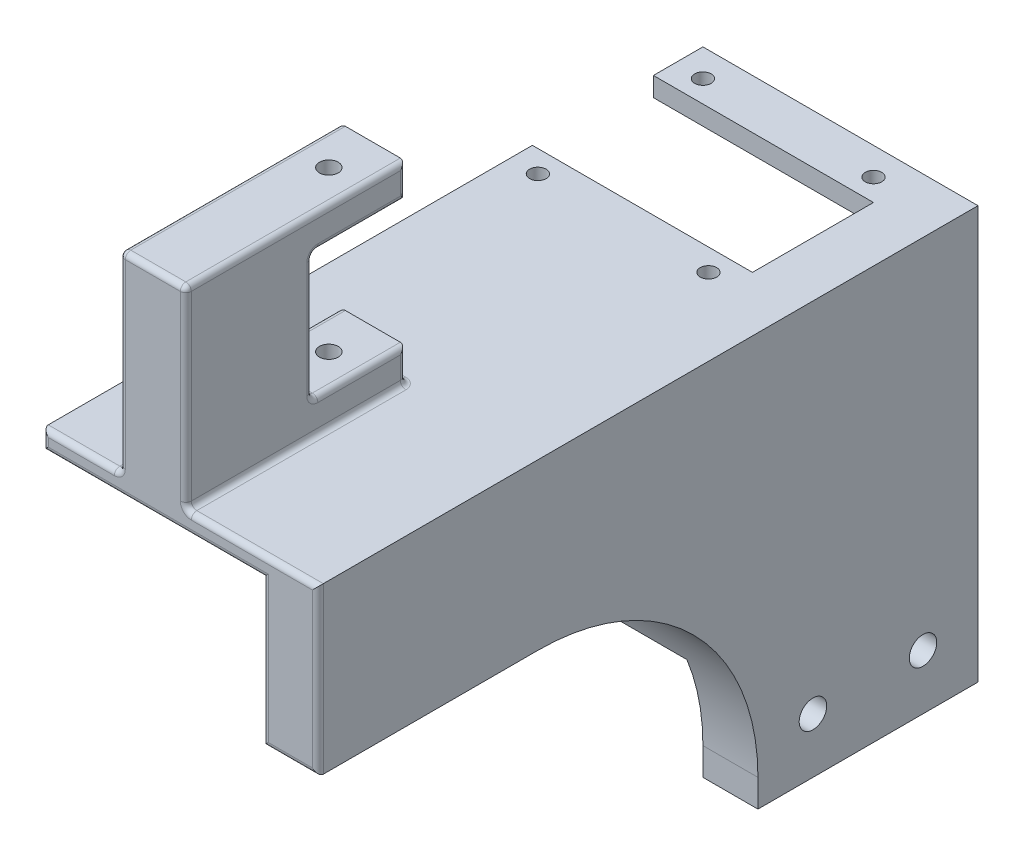
SolidWorks part; units mm, degrees
ref_plane "Front Plane" through (0, 0, 0) normal (0, 0, 1) x (1, 0, 0)
ref_plane "Top Plane" through (0, 0, 0) normal (0, 1, 0) x (1, 0, 0)
ref_plane "Right Plane" through (0, 0, 0) normal (1, 0, 0) x (0, 0, -1)
sketch "Sketch1" plane through (0, 0, 0) normal (1, 0, 0) x (0, 0, -1)
  line L0 (0, 27.5) -> (0, -27.5) construction
  line L5 (-20, 55) -> (20, 55)
  line L6 (-20, 55) -> (-20, 0)
  line L7 (-20, 0) -> (20, 0)
  line L8 (20, 55) -> (20, 0)
  line L9 (-20, 55) -> (20, 0) construction
  line L10 (-20, 0) -> (20, 55) construction
  line L11 (27.5, 0) -> (-27.5, 0) construction
  line L13 (-20, -20) -> (20, -20)
  line L14 (-20, -20) -> (-20, 0)
  line L15 (-20, 0) -> (20, 0)
  line L16 (20, -20) -> (20, 0)
  line L17 (-20, -20) -> (20, 0) construction
  line L18 (-20, 0) -> (20, -20) construction
  line L19 (10, -15) -> (-10, -15) construction
  line L20 (10, -15) -> (10, -5) construction
  line L21 (10, -5) -> (-10, -5) construction
  line L22 (-10, -15) -> (-10, -5) construction
  line L23 (10, -15) -> (-10, -5) construction
  line L24 (10, -5) -> (-10, -15) construction
  circle A0 centre (-10, -10) radius 2.5
  circle A1 centre (10, -10) radius 2.5
  point P1 (0, 27.5)
  point P10 (0, -10)
  point P11 (0, -10)
  dimension "D5" = 5
  dimension "D1" = 55
  dimension "D2" = 40
  dimension "D3" = 20
  dimension "D4" = 20
extrude "Boss-Extrude1" add sketch "Sketch1" along normal blind 10 contours L8 L5 L6 L7 | L13 L16 L7 L14 A1 A0
sketch "Sketch3" plane through (0, 0, 0) normal (-1, 0, 0) x (0, 0, 1)
  line L0 (20, 55) -> (20, -20) construction
  line L1 (-20, 10) -> (20, 10)
  line L2 (-20, 10) -> (-20, 0)
  line L3 (-20, 0) -> (20, 0)
  line L4 (20, 10) -> (20, 0)
  line L5 (-20, 10) -> (20, 0) construction
  line L6 (-20, 0) -> (20, 10) construction
  dimension "D1" = 10
extrude "Boss-Extrude2" add sketch "Sketch3" along normal blind 40
sketch "Sketch4" plane through (0, 0, 0) normal (-1, 0, 0) x (0, 0, 1)
  line L13 (-20, 55) -> (-11, 55)
  line L14 (-20, 55) -> (-20, 51.5)
  line L15 (-20, 51.5) -> (-11, 51.5)
  line L16 (-11, 55) -> (-11, 51.5)
  dimension "D1" = 9
  dimension "D2" = 3.5
extrude "Boss-Extrude3" add sketch "Sketch4" along normal blind 40
sketch "Sketch5" plane through (0, 55, 0) normal (0, 1, 0) x (1, 0, 0)
  line L1 (-40, 20) -> (-35, 20) construction
  line L2 (-40, 20) -> (-40, 15) construction
  line L3 (-40, 15) -> (-35, 15) construction
  line L4 (-35, 20) -> (-35, 15) construction
  line L5 (10, 20) -> (-40, 20) construction
  line L7 (1, 20) -> (-4, 20) construction
  line L8 (1, 20) -> (1, 15) construction
  line L9 (1, 15) -> (-4, 15) construction
  line L10 (-4, 20) -> (-4, 15) construction
  circle A0 centre (-35, 15) radius 1.5
  circle A1 centre (-4, 15) radius 1.5
  dimension "D3" = 3
  dimension "D7" = 3
  dimension "D1" = 5
  dimension "D2" = 5
  dimension "D4" = 5
  dimension "D5" = 5
  dimension "D6" = 31
extrude "Cut-Extrude1" cut sketch "Sketch5" against normal up to next (3.5 mm away)
mirror "Mirror2" about plane through (0, 0, 0) normal (0, 0, 1) of "Cut-Extrude1", "Boss-Extrude3"
sketch "Sketch7" plane through (0, 0, 20) normal (0, 0, 1) x (1, 0, 0)
  line L0 (0, -22) -> (0, 22) construction
  line L1 (-40, 55) -> (0, 55)
  line L2 (-40, 55) -> (-40, 51.5)
  line L3 (-40, 51.5) -> (0, 51.5)
  line L4 (0, 55) -> (0, 51.5)
  line L5 (-20, 51.5) -> (-20, 55) construction
  line L6 (-40, 53.25) -> (0, 53.25) construction
  line L7 (-40, 51.5) -> (0, 51.5) construction
  line L8 (10, 55) -> (10, -20) construction
  line L9 (0, 55) -> (10, 55)
  line L10 (0, 55) -> (0, 25)
  line L11 (0, 25) -> (10, 25)
  line L12 (10, 55) -> (10, 25)
  line L13 (5, 25) -> (5, 55) construction
  line L14 (0, 40) -> (10, 40) construction
  point P199 (5, 40)
  point P296 (-20, 53.25)
  line M2 (10, 55) -> (-40, 55)
  line M3 (-40, 55) -> (-40, 51.5)
  line M4 (-40, 51.5) -> (0, 51.5)
  line M5 (0, 51.5) -> (0, 10)
  line M11 (10, -20) -> (10, 55)
  dimension "D1" = 30
extrude "Boss-Extrude4" add sketch "Sketch7" along normal blind 80 contours L4 M2 M3 M4 | L11 L4 M5 M11 M2
sketch "Sketch8" plane through (0, 55, 0) normal (0, 1, 0) x (1, 0, 0)
  line L0 (10, -100) -> (-40, -100) construction
  line L1 (-26, -100) -> (-14, -100)
  line L2 (-26, -100) -> (-26, -60)
  line L3 (-26, -60) -> (-14, -60)
  line L4 (-14, -100) -> (-14, -60)
  line L5 (-20, -60) -> (-20, -100) construction
  line L6 (-26, -80) -> (-14, -80) construction
  line L7 (-40, -11) -> (-40, -100) construction
  line L8 (0, -22) -> (0, 22) construction
  point P100 (-20, -80)
  dimension "D1" = 12
  dimension "D2" = 40
extrude "Boss-Extrude5" add sketch "Sketch8" along normal blind 35
sketch "Sketch9" plane through (0, 0, 60) normal (0, 0, -1) x (-1, 0, 0)
  line L0 (14, 90) -> (14, 55) construction
  line L1 (14, 84) -> (26, 84)
  line L2 (14, 84) -> (14, 61)
  line L3 (14, 61) -> (26, 61)
  line L4 (26, 84) -> (26, 61)
  line L5 (20, 61) -> (20, 84) construction
  line L6 (14, 72.5) -> (26, 72.5) construction
  line L7 (26, 90) -> (26, 55) construction
  line L8 (14, 90) -> (26, 90) construction
  line L9 (-10, 55) -> (40, 55) construction
  point P172 (20, 72.5)
  dimension "D1" = 6
  dimension "D2" = 6
extrude "Cut-Extrude2" cut sketch "Sketch9" against normal blind 17
sketch "Sketch10" plane through (0, 90, 0) normal (0, 1, 0) x (1, 0, 0)
  line L0 (-20, -1038.2105) -> (-20, 48961.7895) construction
  line L1 (-26, -60) -> (-26, -100) construction
  line L2 (-14, -100) -> (-14, -60) construction
  line L4 (-14, -60) -> (-26, -60) construction
  circle A0 centre (-20, -68) radius 1.7
  dimension "D1" = 3.4
  dimension "D2" = 8
extrude "Cut-Extrude3" cut sketch "Sketch10" against normal up to surface (38.5 mm away) and the other way through all contours A0 up to face at (-35, 51.5, 13.5)
fillet "Fillet1" radius 1 27 edges at (-33, 55, 100) (-26, 55, 80) (-26, 87, 60) (-26, 72.5, 100) (-14, 55, 80) (-14, 72.5, 100) (-20, 55, 60) (-14, 87, 60) (-26, 90, 80) (-20, 90, 100) (-14, 90, 80) (-26, 58, 60) (-14, 58, 60) (-14, 72.5, 77) (-14, 61, 68.5) (-20, 84, 77) (-14, 84, 68.5) (-26, 72.5, 77) (-26, 84, 68.5) (-20, 61, 77) (-26, 61, 68.5) (-20, 51.5, 100) (0, 38.25, 100) (5, 25, 100) (10, 40, 100) (-2, 55, 100) (-40, 53.25, 100)
fillet "Fillet2" radius 40 1 edges at (5, 25, 20)
